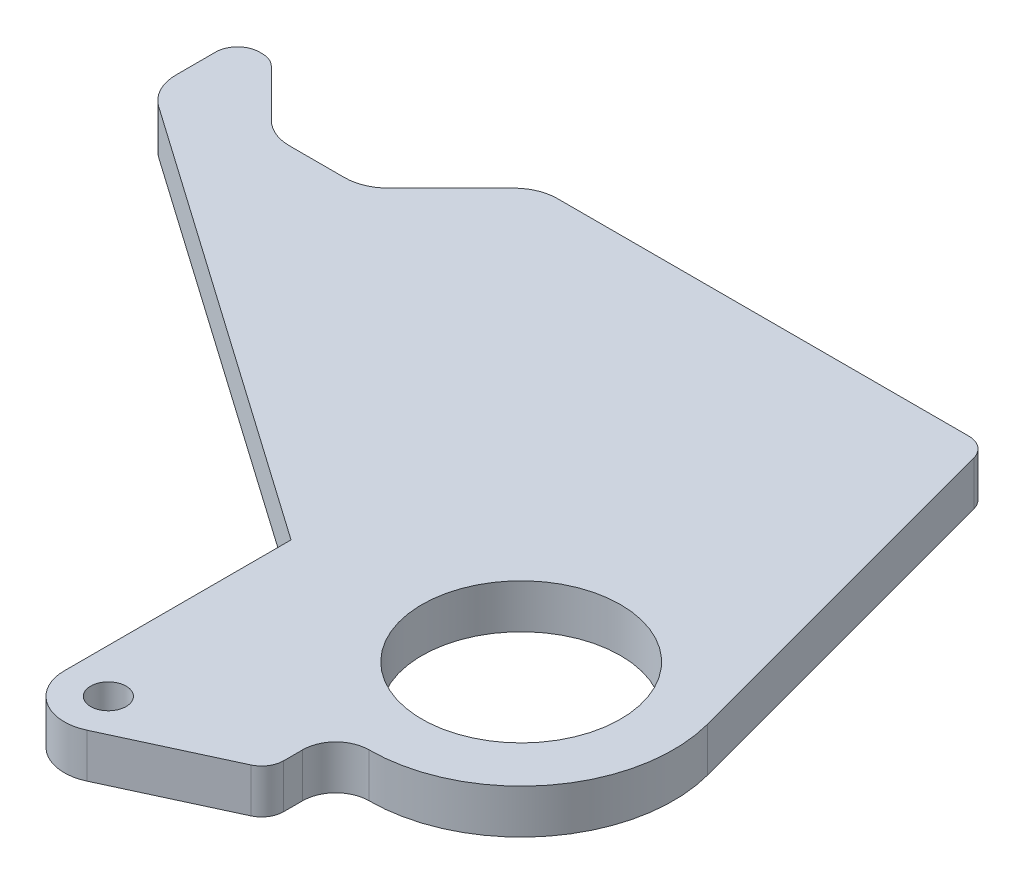
SolidWorks part; units mm, degrees
ref_plane "Front Plane" through (0, 0, 0) normal (0, 0, 1) x (1, 0, 0)
ref_plane "Top Plane" through (0, 0, 0) normal (0, 1, 0) x (1, 0, 0)
ref_plane "Right Plane" through (0, 0, 0) normal (1, 0, 0) x (0, 0, -1)
sketch "Sketch1" plane through (0, 0, 0) normal (0, 1, 0) x (1, 0, 0)
  line L0 (4.08, -3.175) -> (-55.0879, -3.175)
  line L1 (-59.578, -5.0349) -> (-68.5582, -14.0151)
  line L2 (-73.0484, -15.875) -> (-80.9391, -15.875)
  line L3 (-85.4293, -14.0151) -> (-92.1645, -7.2799)
  line L4 (-94.4095, -6.35) -> (-94.7738, -6.35)
  line L5 (-97.9488, -9.525) -> (-97.9488, -15.2009)
  line L6 (-95.241, -20.4025) -> (-31.75, -64.8593)
  line L7 (-31.75, -64.8593) -> (-31.75, -97.4852)
  line L8 (-22.7333, -103.2481) -> (-6.6042, -95.7847)
  line L9 (-4.7625, -92.9032) -> (-4.7625, -90.17)
  line L10 (21.161, -57.8299) -> (7.1468, -5.5282)
  circle A0 centre (-25.4, -97.4852) radius 2.5527
  circle A1 centre (0, -63.5) radius 14.2875
  arc A2 (-55.0879, -3.175) -> (-59.578, -5.0349) centre (-55.0879, -9.525) ccw
  arc A3 (-68.5582, -14.0151) -> (-73.0484, -15.875) centre (-73.0484, -9.525) cw
  arc A4 (-80.9391, -15.875) -> (-85.4293, -14.0151) centre (-80.9391, -9.525) cw
  arc A5 (-92.1645, -7.2799) -> (-94.4095, -6.35) centre (-94.4095, -9.525) ccw
  arc A6 (-94.7738, -6.35) -> (-97.9488, -9.525) centre (-94.7738, -9.525) ccw
  arc A7 (-97.9488, -15.2009) -> (-95.241, -20.4025) centre (-91.5988, -15.2009) ccw
  arc A8 (-31.75, -97.4852) -> (-22.7333, -103.2481) centre (-25.4, -97.4852) ccw
  arc A9 (-6.6042, -95.7847) -> (-4.7625, -92.9032) centre (-7.9375, -92.9032) ccw
  arc A10 (-4.7625, -90.17) -> (0, -85.4075) centre (0, -90.17) cw
  arc A11 (0, -85.4075) -> (21.161, -57.8299) centre (0, -63.5) ccw
  arc A12 (7.1468, -5.5282) -> (4.08, -3.175) centre (4.08, -6.35) ccw
  dimension "D1" = 5.1054
  dimension "D2" = 28.575
  dimension "D3" = 6.35
  dimension "D4" = 6.35
  dimension "D5" = 3.175
  dimension "D6" = 2.7078
  dimension "D7" = 3.5392
  dimension "D8" = 6.35
  dimension "D9" = 6.35
  dimension "D10" = 3.175
  dimension "D11" = 4.7625
  dimension "D12" = 21.9075
  dimension "D13" = 5.7843
  dimension "D14" = 24.9004
  dimension "D15" = 66.1988
  dimension "D16" = 75.2154
  dimension "D17" = 90.0113
  dimension "D18" = 102.0288
  dimension "D19" = 105.0956
  dimension "D20" = 12.0259
  dimension "D21" = 89.7282
extrude "Boss-Extrude1" add sketch "Sketch1" against normal blind 6.35
